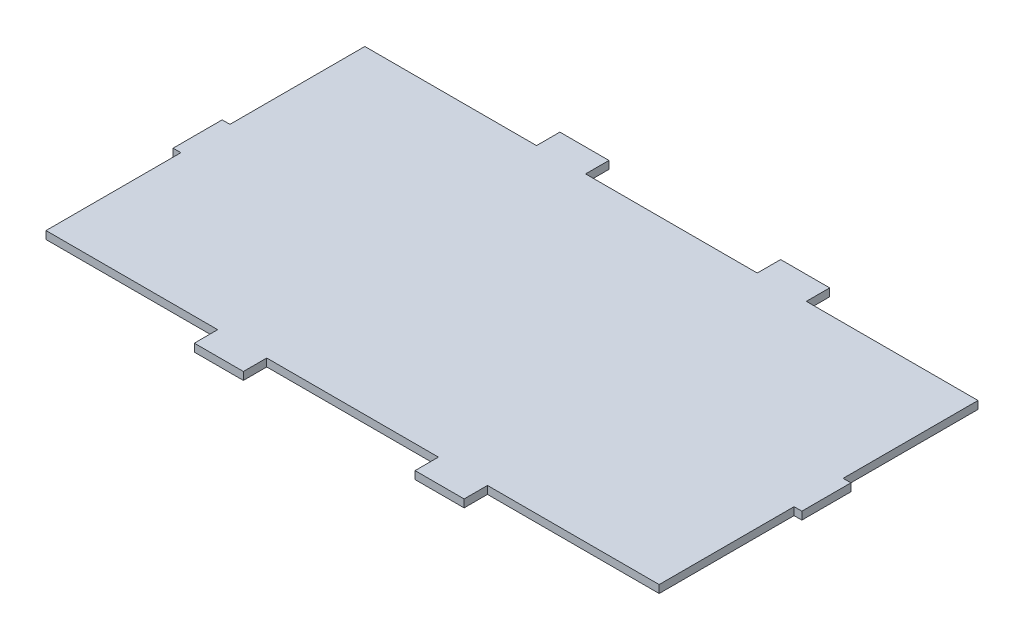
SolidWorks part; units mm, degrees
ref_plane "Plan de face" through (0, 0, 0) normal (0, 0, 1) x (1, 0, 0)
ref_plane "Plan de dessus" through (0, 0, 0) normal (0, 1, 0) x (1, 0, 0)
ref_plane "Plan de droite" through (0, 0, 0) normal (1, 0, 0) x (0, 0, -1)
sketch "Esquisse1" plane through (0, 0, 0) normal (0, 1, 0) x (1, 0, 0)
  line L1 (0, 0) -> (250, 0)
  line L2 (0, 0) -> (0, 130)
  line L3 (0, 130) -> (250, 130)
  line L4 (250, 0) -> (250, 130)
  dimension "D1" = 250
  dimension "D2" = 130
extrude "Boss.-Extru.1" add sketch "Esquisse1" along normal blind 3.175
sketch "Esquisse2" plane through (0, 3.175, 0) normal (0, 1, 0) x (1, 0, 0)
  line L0 (0, 130) -> (0, 0) construction
  line L1 (0, 75) -> (-3.175, 75)
  line L2 (0, 75) -> (0, 55)
  line L3 (0, 55) -> (-3.175, 55)
  line L4 (-3.175, 75) -> (-3.175, 55)
  line L5 (250, 130) -> (0, 130) construction
  line L6 (0, 0) -> (250, 0) construction
  line L7 (250, 0) -> (250, 130) construction
  line L8 (250, 75) -> (253.175, 75)
  line L9 (250, 75) -> (250, 55)
  line L10 (250, 55) -> (253.175, 55)
  line L11 (253.175, 75) -> (253.175, 55)
  line L13 (70, 130) -> (90, 130)
  line L14 (70, 130) -> (70, 139.525)
  line L15 (70, 139.525) -> (90, 139.525)
  line L16 (90, 130) -> (90, 139.525)
  line L17 (180, 130) -> (160, 130)
  line L18 (180, 130) -> (180, 139.525)
  line L19 (180, 139.525) -> (160, 139.525)
  line L20 (160, 130) -> (160, 139.525)
  line L21 (180, 0) -> (160, 0)
  line L22 (180, 0) -> (180, -9.525)
  line L23 (180, -9.525) -> (160, -9.525)
  line L24 (160, 0) -> (160, -9.525)
  line L25 (90, 0) -> (70, 0)
  line L26 (90, 0) -> (90, -9.525)
  line L27 (90, -9.525) -> (70, -9.525)
  line L28 (70, 0) -> (70, -9.525)
  dimension "D1" = 55
  dimension "D2" = 55
  dimension "D3" = 3.175
  dimension "D4" = 3.175
  dimension "D5" = 70
  dimension "D6" = 20
  dimension "D7" = 9.525
  dimension "D8" = 70
  dimension "D9" = 20
  dimension "D10" = 9.525
  dimension "D11" = 9.525
  dimension "D12" = 9.525
extrude "Boss.-Extru.2" add sketch "Esquisse2" against normal blind 3.175
